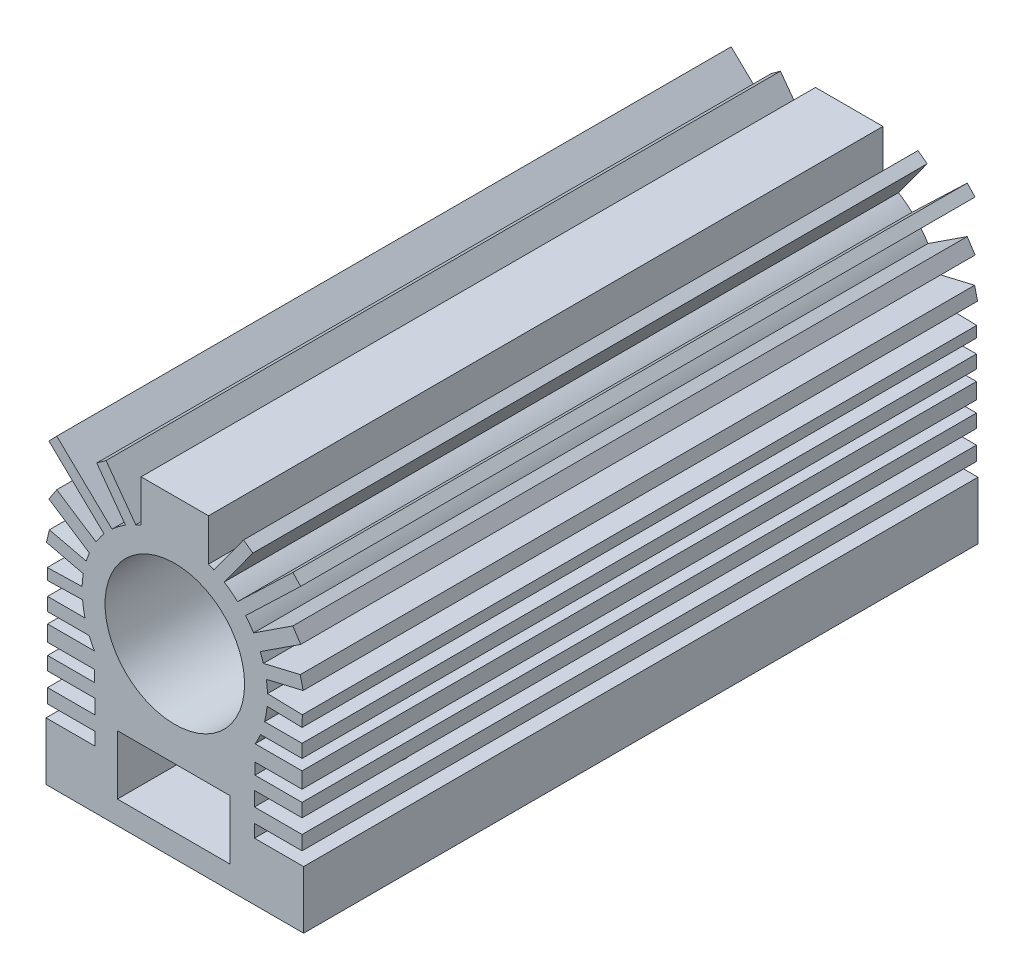
SolidWorks part; units mm, degrees
ref_plane "Front Plane" through (0, 0, 0) normal (0, 0, 1) x (1, 0, 0)
ref_plane "Top Plane" through (0, 0, 0) normal (0, 1, 0) x (1, 0, 0)
ref_plane "Right Plane" through (0, 0, 0) normal (1, 0, 0) x (0, 0, -1)
sketch "Sketch1" plane through (0, 0, 0) normal (0, 0, 1) x (1, 0, 0)
  line L0 (-17.8913, 17.0453) -> (69.4376, 17.0453) construction
  line L1 (-182.7266, 44.5438) -> (-95.3976, 44.5438) construction
  line L2 (1.0039, -24.3628) -> (1.0039, -51.6489) construction
  line L7 (-9.8221, -25.6614) -> (-5.0829, -30.205)
  line L8 (-3.9327, -44.2872) -> (5.7317, -44.2872)
  line L9 (-3.9327, -44.2872) -> (-3.9327, -49.3811)
  line L10 (-3.9327, -49.3811) -> (5.7317, -49.3811)
  line L11 (5.7317, -44.2872) -> (5.7317, -49.3811)
  line L14 (-5.9044, -51.3678) -> (1.0039, -51.3678)
  line L17 (-1.8965, -27.9671) -> (-1.8965, -24.3628)
  line L18 (-1.8965, -24.3628) -> (3.9043, -24.3628)
  line L20 (-10.0735, -51.3678) -> (-5.9044, -51.3678)
  line L21 (-10.0735, -51.3678) -> (-10.0735, -46.4026)
  line L22 (-10.0735, -46.4026) -> (-5.8475, -46.4026)
  line L24 (-9.8221, -25.6614) -> (-9.1476, -24.9579)
  line L26 (-9.1476, -24.9579) -> (-4.3971, -29.5124)
  line L27 (-9.8236, -29.9807) -> (-9.1454, -28.9438)
  line L28 (-9.8236, -29.9807) -> (-6.3442, -32.2564)
  line L29 (-9.1454, -28.9438) -> (-5.7711, -31.1508)
  line L32 (-6.866, -34.0607) -> (-10.0344, -33.3122)
  line L33 (-6.6151, -32.999) -> (-9.7836, -32.2505)
  line L34 (-10.0344, -33.3122) -> (-9.7836, -32.2505)
  line L36 (-6.9671, -35.0743) -> (-9.9636, -35.1487)
  line L37 (-6.9269, -36.0338) -> (-9.9398, -36.1095)
  line L38 (-9.9636, -35.1487) -> (-9.9398, -36.1095)
  line L39 (-9.9398, -37.2886) -> (-9.9398, -38.4201)
  line L40 (-9.9398, -37.2886) -> (-6.7179, -37.2886)
  line L41 (-9.9398, -38.4201) -> (-6.362, -38.4201)
  line L43 (-9.9398, -39.3417) -> (-9.9398, -40.7097)
  line L44 (-9.9398, -39.3417) -> (-5.9071, -39.3417)
  line L45 (-9.9398, -40.7097) -> (-5.9071, -40.7097)
  line L47 (-9.9398, -41.6884) -> (-9.9398, -42.8421)
  line L48 (-9.9398, -41.6884) -> (-5.8896, -41.6884)
  line L49 (-9.9398, -42.8421) -> (-5.8475, -42.8421)
  line L51 (-9.9398, -44.0791) -> (-9.9398, -45.2995)
  line L52 (-9.9398, -44.0791) -> (-5.8475, -44.0791)
  line L53 (-9.9398, -45.2995) -> (-5.8475, -45.2995)
  line L55 (-5.7083, -25.2369) -> (-4.9098, -24.6556)
  line L56 (-5.7083, -25.2369) -> (-3.2411, -28.6258)
  line L57 (-4.9098, -24.6556) -> (-2.3555, -28.1642)
  line L58 (-5.8475, -45.2995) -> (-5.8475, -46.4026)
  line L59 (-5.8475, -44.0791) -> (-5.8475, -42.8421)
  line L60 (-5.9071, -40.7097) -> (-5.8896, -41.6884)
  line L61 (7.9149, -40.7097) -> (7.8975, -41.6884)
  line L62 (7.8554, -44.0791) -> (7.8554, -42.8421)
  line L63 (7.8554, -45.2995) -> (7.8554, -46.4026)
  line L64 (6.9177, -24.6556) -> (4.3633, -28.1642)
  line L65 (7.7162, -25.2369) -> (5.249, -28.6258)
  line L66 (7.7162, -25.2369) -> (6.9177, -24.6556)
  line L67 (11.9476, -45.2995) -> (7.8554, -45.2995)
  line L68 (11.9476, -44.0791) -> (7.8554, -44.0791)
  line L69 (11.9476, -44.0791) -> (11.9476, -45.2995)
  line L70 (11.9476, -42.8421) -> (7.8554, -42.8421)
  line L71 (11.9476, -41.6884) -> (7.8975, -41.6884)
  line L72 (11.9476, -41.6884) -> (11.9476, -42.8421)
  line L73 (11.9476, -40.7097) -> (7.9149, -40.7097)
  line L74 (11.9476, -39.3417) -> (7.9149, -39.3417)
  line L75 (11.9476, -39.3417) -> (11.9476, -40.7097)
  line L76 (11.9476, -38.4201) -> (8.3698, -38.4201)
  line L77 (11.9476, -37.2886) -> (8.7257, -37.2886)
  line L78 (11.9476, -37.2886) -> (11.9476, -38.4201)
  line L79 (11.9714, -35.1487) -> (11.9476, -36.1095)
  line L80 (8.9348, -36.0338) -> (11.9476, -36.1095)
  line L81 (8.9749, -35.0743) -> (11.9714, -35.1487)
  line L82 (12.0422, -33.3122) -> (11.7914, -32.2505)
  line L83 (8.6229, -32.999) -> (11.7914, -32.2505)
  line L84 (8.8738, -34.0607) -> (12.0422, -33.3122)
  line L85 (11.1532, -28.9438) -> (7.779, -31.1508)
  line L86 (11.8314, -29.9807) -> (8.352, -32.2564)
  line L87 (11.8314, -29.9807) -> (11.1532, -28.9438)
  line L88 (11.1555, -24.9579) -> (6.405, -29.5124)
  line L89 (11.8299, -25.6614) -> (11.1555, -24.9579)
  line L90 (12.0813, -46.4026) -> (7.8554, -46.4026)
  line L91 (12.0813, -51.3678) -> (12.0813, -46.4026)
  line L92 (12.0813, -51.3678) -> (7.9122, -51.3678)
  line L93 (3.9043, -27.9671) -> (3.9043, -24.3628)
  line L94 (7.9122, -51.3678) -> (1.0039, -51.3678)
  line L96 (11.8299, -25.6614) -> (7.0908, -30.205)
  circle A0 centre (1.0039, -35.3574) radius 6
  arc A2 (-5.0829, -30.205) -> (-5.7711, -31.1508) centre (1.0039, -35.3574) ccw
  arc A3 (-4.3971, -29.5124) -> (-3.2411, -28.6258) centre (1.0039, -35.3574) cw
  arc A4 (-1.8965, -27.9671) -> (-2.3555, -28.1642) centre (1.0039, -35.3574) ccw
  arc A5 (-6.3442, -32.2564) -> (-6.6151, -32.999) centre (1.0039, -35.3574) ccw
  arc A6 (-6.866, -34.0607) -> (-6.9671, -35.0743) centre (1.0039, -35.3574) ccw
  arc A7 (-6.9269, -36.0338) -> (-6.7179, -37.2886) centre (1.0039, -35.3574) ccw
  arc A8 (-6.362, -38.4201) -> (-5.9071, -39.3417) centre (1.0039, -35.3574) ccw
  arc A9 (8.3698, -38.4201) -> (7.9149, -39.3417) centre (1.0039, -35.3574) cw
  arc A10 (8.9348, -36.0338) -> (8.7257, -37.2886) centre (1.0039, -35.3574) cw
  arc A11 (8.8738, -34.0607) -> (8.9749, -35.0743) centre (1.0039, -35.3574) cw
  arc A12 (8.352, -32.2564) -> (8.6229, -32.999) centre (1.0039, -35.3574) cw
  arc A13 (3.9043, -27.9671) -> (4.3633, -28.1642) centre (1.0039, -35.3574) cw
  arc A14 (6.405, -29.5124) -> (5.249, -28.6258) centre (1.0039, -35.3574) ccw
  arc A15 (7.0908, -30.205) -> (7.779, -31.1508) centre (1.0039, -35.3574) cw
  point P16 (-6.9671, -35.3574)
  point P17 (1.0039, -51.3678)
  point P20 (0, 0)
  point P31 (0, 0)
  point P61 (-5.9072, -39.3417)
  point P94 (0, 0)
  point P97 (-6.7179, -37.2794)
  point P107 (0, 0)
  point P109 (1.0039, -24.3628)
  point P110 (1.0039, -51.3678)
  dimension "D3" = 12
extrude "Boss-Extrude1" add sketch "Sketch1" along normal blind 58
sketch "Sketch2" plane through (0, -51.3678, 0) normal (0, -1, 0) x (1, 0, 0)
  line L0 (1.0039, 58) -> (1.3728, 0) construction
  line L1 (-10.0735, 58) -> (12.0813, 58) construction
  line L2 (-10.0735, 0) -> (12.0813, 0) construction
  line L3 (-10.0735, 29) -> (12.0813, 29) construction
  line L4 (-10.0735, 58) -> (-10.0735, 0) construction
  line L5 (12.0813, 58) -> (12.0813, 0) construction
  circle A0 centre (1.1884, 29) radius 2.5
  circle A1 centre (-6.5735, 10) radius 1.5576
  circle A2 centre (9.1913, 10.1003) radius 1.5576
  circle A3 centre (9.1913, 47.8997) radius 1.5576
  circle A4 centre (-6.5735, 48) radius 1.5576
  point P16 (0, 0)
  point P17 (-6.3654, 3.8293)
  dimension "D1" = 5
  dimension "D2" = 3.1153
  dimension "D3" = 3.5
  dimension "D4" = 10
extrude "Cut-Extrude1" cut sketch "Sketch2" against normal blind 10
